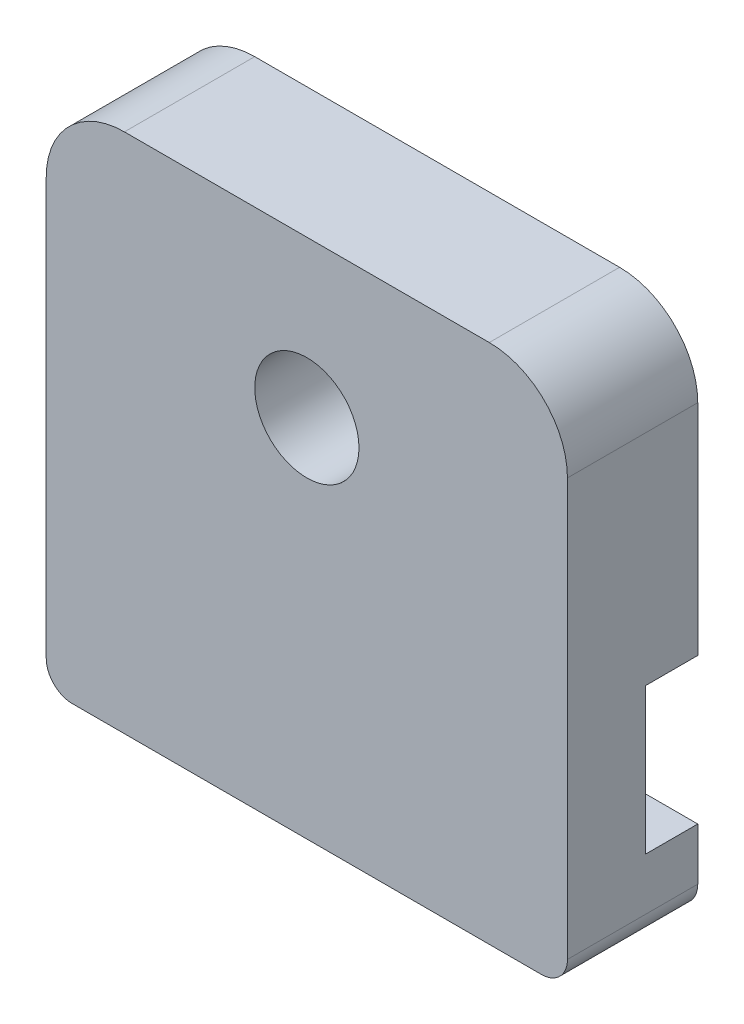
SolidWorks part; units mm, degrees
ref_plane "Front Plane" through (0, 0, 0) normal (0, 0, 1) x (1, 0, 0)
ref_plane "Top Plane" through (0, 0, 0) normal (0, 1, 0) x (1, 0, 0)
ref_plane "Right Plane" through (0, 0, 0) normal (1, 0, 0) x (0, 0, -1)
sketch "Sketch1" plane through (0, 0, 0) normal (0, 0, 1) x (1, 0, 0)
  line L1 (-10, -10) -> (10, -10)
  line L2 (-10, -10) -> (-10, 10)
  line L3 (-10, 10) -> (10, 10)
  line L4 (10, -10) -> (10, 10)
  line L5 (-10, -10) -> (10, 10) construction
  line L6 (-10, 10) -> (10, -10) construction
  point P0 (0, 0)
  dimension "D1" = 20
  dimension "D2" = 20
extrude "Boss-Extrude1" add sketch "Sketch1" along normal blind 5
sketch "Sketch2" plane through (0, 0, 5) normal (0, 0, 1) x (1, 0, 0)
  line L0 (10, 10) -> (-10, 10) construction
  circle A0 centre (0, 4) radius 2
  point P0 (0, 10)
  dimension "D1" = 4
  dimension "D2" = 6
extrude "Cut-Extrude1" cut sketch "Sketch2" against normal through all
fillet "Fillet1" radius 3 2 edges at (-10, 10, 2.5) (10, 10, 2.5)
fillet "Fillet2" radius 1 2 edges at (10, -10, 2.5) (-10, -10, 2.5)
sketch "Sketch3" plane through (0, 0, 0) normal (0, 0, -1) x (-1, 0, 0)
  line L0 (-10, -9) -> (-10, 7) construction
  line L1 (-10, -7) -> (10, -7)
  line L2 (-10, -7) -> (-10, -1.4)
  line L3 (-10, -1.4) -> (10, -1.4)
  line L4 (10, -7) -> (10, -1.4)
  line L5 (10, 7) -> (10, -9) construction
  line L6 (9, -10) -> (-9, -10) construction
  dimension "D1" = 5.6
  dimension "D2" = 3
extrude "Cut-Extrude2" cut sketch "Sketch3" against normal blind 2
